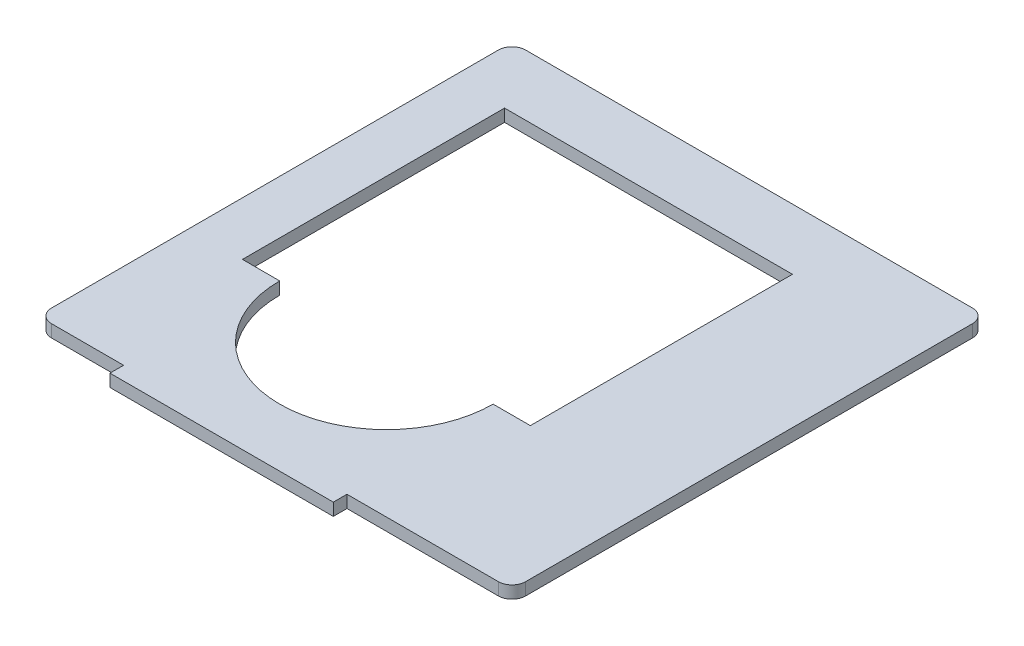
SolidWorks part; units mm, degrees
ref_plane "Front Plane" through (0, 0, 0) normal (0, 0, 1) x (1, 0, 0)
ref_plane "Top Plane" through (0, 0, 0) normal (0, 1, 0) x (1, 0, 0)
ref_plane "Right Plane" through (0, 0, 0) normal (1, 0, 0) x (0, 0, -1)
sketch "Sketch1" plane through (0, 0, 0) normal (0, 1, 0) x (1, 0, 0)
  line L1 (90, 95.5) -> (-90, 95.5)
  line L2 (95.5, 90) -> (95.5, -90)
  line L3 (90, -95.5) -> (-90, -95.5)
  line L4 (-95.5, 90) -> (-95.5, -90)
  line L5 (95.5, 95.5) -> (-95.5, -95.5) construction
  line L6 (95.5, -95.5) -> (-95.5, 95.5) construction
  arc A0 (95.5, -90) -> (90, -95.5) centre (90, -90) cw
  arc A1 (-90, -95.5) -> (-95.5, -90) centre (-90, -90) cw
  arc A2 (-90, 95.5) -> (-95.5, 90) centre (-90, 90) ccw
  arc A3 (90, 95.5) -> (95.5, 90) centre (90, 90) cw
  point P0 (0, 0)
  dimension "D2" = 5.5
  dimension "D1" = 191
extrude "Boss-Extrude1" add sketch "Sketch1" along normal mid plane 5
sketch "Sketch2" plane through (0, 2.5, 0) normal (0, 1, 0) x (1, 0, 0)
  line L1 (42, 71) -> (-74, 71)
  line L2 (42, 71) -> (42, -34.6102)
  line L4 (-74, 71) -> (-74, -34.6102)
  line L5 (42, 71) -> (-74, -140.2205) construction
  line L6 (42, -140.2205) -> (-74, 71) construction
  line L8 (-90, 100) -> (90, 100) construction
  line L9 (-16, -34.6102) -> (-81.1816, -34.6102) construction
  line L10 (-81.1816, -34.6102) -> (44.8599, -34.6102) construction
  line L11 (27, -34.6102) -> (42, -34.6102)
  line L12 (-59, -34.6102) -> (-74, -34.6102)
  arc A0 (42, -34.6102) -> (-74, -34.6102) centre (-16, -34.6102) cw construction
  arc A1 (27, -34.6102) -> (-59, -34.6102) centre (-16, -34.6102) cw
  point P0 (-16, -34.6102)
  dimension "D1" = 116
  dimension "D2" = 29
  dimension "D4" = 58
  dimension "D3" = 15
extrude "Cut-Extrude1" cut sketch "Sketch2" against normal through all contours L2 L11 A1 L12 L4 L1
sketch "Sketch3" plane through (0, 2.5, 0) normal (0, 1, 0) x (1, 0, 0)
  line L0 (-90, -95.5) -> (90, -95.5) construction
  line L1 (-61, -101) -> (29, -101)
  line L2 (-61, -101) -> (-61, -95.5)
  line L3 (-61, -95.5) -> (29, -95.5)
  line L4 (29, -101) -> (29, -95.5)
  line L5 (29, -95.5) -> (29, -101) construction
extrude "Boss-Extrude2" add sketch "Sketch3" against normal up to vertex (5 mm away)
